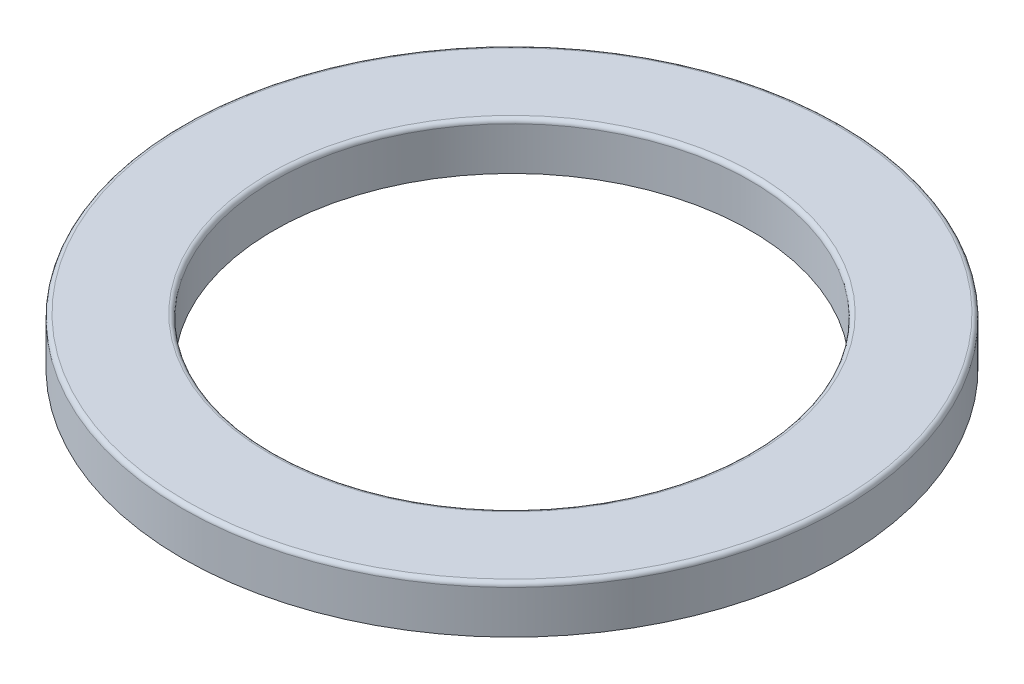
SolidWorks part; units mm, degrees
ref_plane "Front Plane" through (0, 0, 0) normal (0, 0, 1) x (1, 0, 0)
ref_plane "Top Plane" through (0, 0, 0) normal (0, 1, 0) x (1, 0, 0)
ref_plane "Right Plane" through (0, 0, 0) normal (1, 0, 0) x (0, 0, -1)
sketch "Sketch1" plane through (0, 0, 0) normal (0, 1, 0) x (1, 0, 0)
  circle A0 centre (0, 0) radius 85
  circle A1 centre (0, 0) radius 61.5
  dimension "D1" = 170
  dimension "D2" = 123
extrude "Boss-Extrude1" add sketch "Sketch1" along normal blind 12.2
fillet "Fillet1" radius 1.1 2 edges at (0, 12.2, 61.5) (0, 12.2, 85)
sketch "Sketch2" plane through (0, 0, 0) normal (0, 0, 1) x (1, 0, 0)
  line L0 (-85, 0) -> (85, 0) construction
  line L1 (-77.98, 0) -> (-67.02, 0)
  arc A0 (-77.98, 0) -> (-67.02, 0) centre (-72.5, -7.3025) cw
  dimension "D1" = 9.13
  dimension "D2" = 67.02
  dimension "D3" = 77.98
ref_axis "Axis1" through (0, 11.1, 0) along (0, -1, 0)
revolve "Cut-Revolve1" cut sketch "Sketch2" angle 360 about axis through (0, 11.1, 0) along (0, -1, 0)
